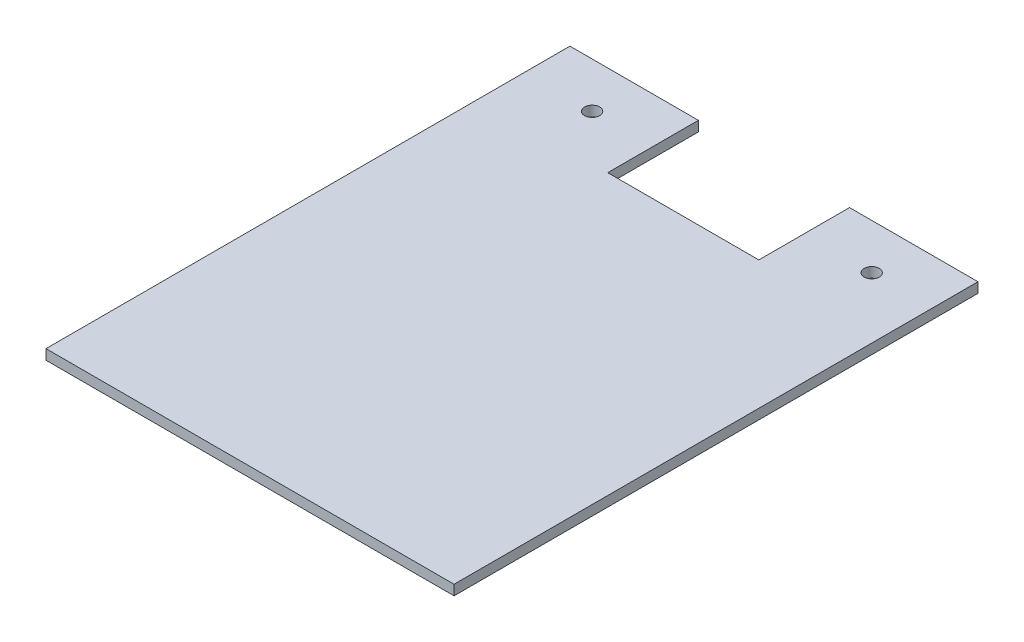
SolidWorks part; units mm, degrees
ref_plane "Alzado" through (0, 0, 0) normal (0, 0, 1) x (1, 0, 0)
ref_plane "Planta" through (0, 0, 0) normal (0, 1, 0) x (1, 0, 0)
ref_plane "Vista lateral" through (0, 0, 0) normal (1, 0, 0) x (0, 0, -1)
sketch "Croquis1" plane through (0, 0, 0) normal (0, 1, 0) x (1, 0, 0)
  line L0 (0, 0) -> (0, 104)
  line L1 (0, 104) -> (-25.5, 104)
  line L2 (-25.5, 104) -> (-25.5, 86)
  line L3 (-25.5, 86) -> (-55.5, 86)
  line L4 (-55.5, 86) -> (-55.5, 104)
  line L5 (-55.5, 104) -> (-81, 104)
  line L6 (-81, 104) -> (-81, 0)
  line L7 (-81, 0) -> (0, 0)
  dimension "D1" = 104
  dimension "D2" = 81
  dimension "D3" = 25.5
  dimension "D4" = 25.5
  dimension "D5" = 18
extrude "Saliente-Extruir1" add sketch "Croquis1" along normal blind 2
sketch "Croquis2" plane through (0, 2, 0) normal (0, 1, 0) x (1, 0, 0)
  line L0 (-55.5, 104) -> (-81, 104) construction
  line L1 (0, 104) -> (-25.5, 104) construction
  line L2 (-55.5, 86) -> (-55.5, 104) construction
  line L3 (0, 0) -> (0, 104) construction
  circle A0 centre (-67.6, 95) radius 1.5
  circle A1 centre (-12.1, 95) radius 1.5
  dimension "D1" = 3
  dimension "D2" = 3
  dimension "D3" = 9
  dimension "D4" = 9
  dimension "D5" = 12.1
  dimension "D6" = 12.1
extrude "Cortar-Extruir1" cut sketch "Croquis2" against normal blind 2
